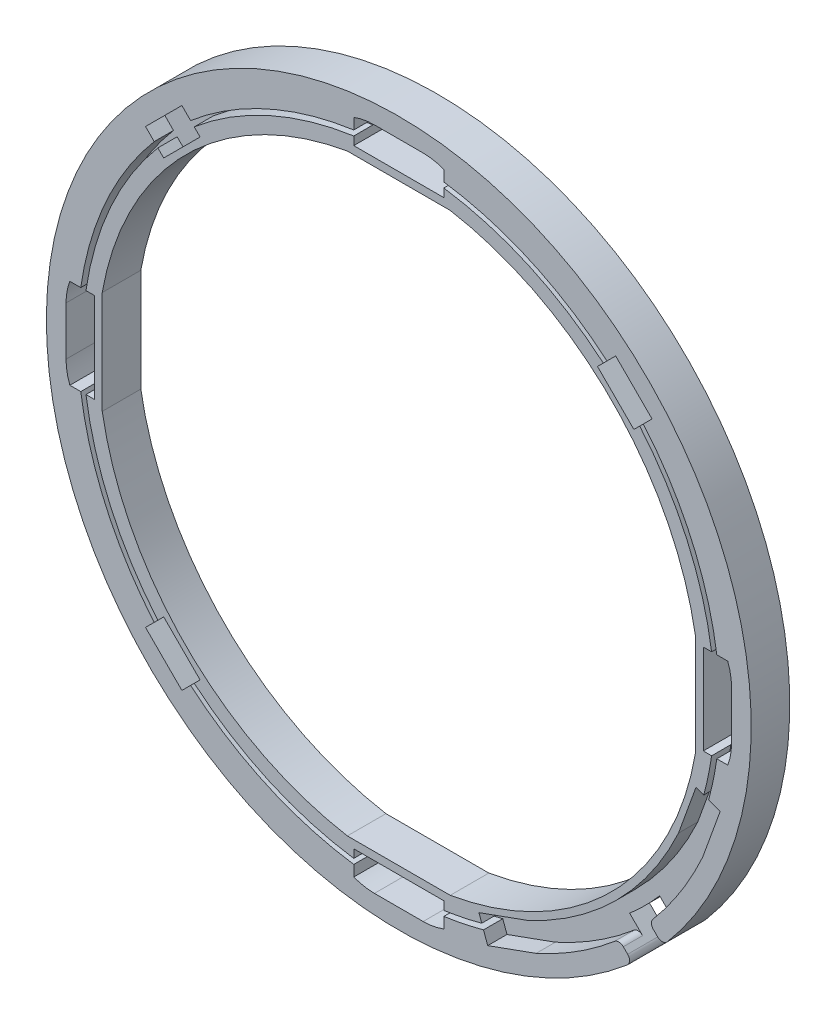
SolidWorks part; units mm, degrees
ref_plane "Front Plane" through (0, 0, 0) normal (0, 0, 1) x (1, 0, 0)
ref_plane "Top Plane" through (0, 0, 0) normal (0, 1, 0) x (1, 0, 0)
ref_plane "Right Plane" through (0, 0, 0) normal (1, 0, 0) x (0, 0, -1)
sketch "Sketch2" plane through (0, 0, 0) normal (0, 0, 1) x (1, 0, 0)
  line L0 (0, 0) -> (0, 31.8027) construction
  line L1 (-4, 23.0556) -> (4, 23.0556)
  line L2 (23.0556, 4) -> (23.0556, -4)
  line L3 (4, -23.0556) -> (-4, -23.0556)
  line L4 (-23.0556, -4) -> (-23.0556, 4)
  circle A0 centre (0, 0) radius 27.4
  arc A1 (-4, 23.0556) -> (-23.0556, 4) centre (0, 0) ccw
  arc A2 (4, 23.0556) -> (0, 23.4) centre (0, 0) ccw construction
  arc A3 (0, 23.4) -> (-4, 23.0556) centre (0, 0) ccw construction
  arc A4 (23.0556, -4) -> (23.0556, 4) centre (0, 0) ccw construction
  arc A5 (23.0556, 4) -> (4, 23.0556) centre (0, 0) ccw
  arc A6 (-4, -23.0556) -> (4, -23.0556) centre (0, 0) ccw construction
  arc A7 (4, -23.0556) -> (23.0556, -4) centre (0, 0) ccw
  arc A8 (-23.0556, 4) -> (-23.0556, -4) centre (0, 0) ccw construction
  arc A9 (-23.0556, -4) -> (-4, -23.0556) centre (0, 0) ccw
  dimension "D1" = 54.8
  dimension "D4" = 4
extrude "Extrude1" add sketch "Sketch2" along normal blind 3
ref_plane "Plane1" through (0, 0, 3) normal (0, 0, 1) x (1, 0, 0)
sketch "Sketch4" plane through (0, 0, 0) normal (1, 0, 0) x (0, 0, -1)
  line L0 (-3, 27.4) -> (-3.3, 23.1028)
  line L1 (-3.3, 23.1028) -> (-3.3, 0)
  line L2 (0, 0) -> (-3, 0) construction
  line L3 (-3, 27.4) -> (-3, -27.4) construction
  line L4 (-3.3, 0) -> (-3, 0)
  line L5 (-3, 0) -> (-3, 27.4)
  dimension "D1" = 0.3
revolve "Cut-Revolve1" [suppressed] cut sketch "Sketch4" angle 360 about L2
sketch "Sketch3" plane through (0, 0, 3) normal (0, 0, 1) x (1, 0, 0)
  line L0 (0, 0) -> (0, 29.437) construction
  line L1 (0, 0) -> (35.1715, 0) construction
  line L2 (-1.8939, 25.8711) -> (1.8939, 25.8711)
  line L3 (3.5, 25.5741) -> (3.5, 23.6711)
  line L4 (3.5, 23.6711) -> (-3.5, 23.6711)
  line L5 (1.8939, 25.8711) -> (3.5, 25.8711) construction
  line L6 (3.5, 25.8711) -> (3.5, 25.5741) construction
  line L7 (-3.5, 25.8711) -> (-3.5, 25.5741) construction
  line L8 (-1.8939, 25.8711) -> (-3.5, 25.8711) construction
  line L9 (-3.5, 25.5741) -> (-3.5, 23.6711)
  line L10 (23.6711, -3.5) -> (23.6711, 3.5)
  line L11 (25.5741, 3.5) -> (23.6711, 3.5)
  line L12 (25.8711, 1.8939) -> (25.8711, -1.8939)
  line L13 (25.5741, -3.5) -> (23.6711, -3.5)
  line L14 (-3.5, -23.6711) -> (3.5, -23.6711)
  line L15 (3.5, -25.5741) -> (3.5, -23.6711)
  line L16 (1.8939, -25.8711) -> (-1.8939, -25.8711)
  line L17 (-3.5, -25.5741) -> (-3.5, -23.6711)
  line L18 (-23.6711, 3.5) -> (-23.6711, -3.5)
  line L19 (-25.5741, -3.5) -> (-23.6711, -3.5)
  line L20 (-25.8711, -1.8939) -> (-25.8711, 1.8939)
  line L21 (-25.5741, 3.5) -> (-23.6711, 3.5)
  arc A0 (1.8939, 25.8711) -> (3.5, 25.5741) centre (1.8939, 21.3807) cw
  arc A1 (-1.8939, 25.8711) -> (-3.5, 25.5741) centre (-1.8939, 21.3807) ccw
  arc A2 (25.8711, 1.8939) -> (25.5741, 3.5) centre (21.3807, 1.8939) ccw
  arc A3 (25.8711, -1.8939) -> (25.5741, -3.5) centre (21.3807, -1.8939) cw
  arc A4 (1.8939, -25.8711) -> (3.5, -25.5741) centre (1.8939, -21.3807) ccw
  arc A5 (-1.8939, -25.8711) -> (-3.5, -25.5741) centre (-1.8939, -21.3807) cw
  arc A6 (-25.8711, -1.8939) -> (-25.5741, -3.5) centre (-21.3807, -1.8939) ccw
  arc A7 (-25.8711, 1.8939) -> (-25.5741, 3.5) centre (-21.3807, 1.8939) cw
  point P12 (0, 23.6711)
  point P13 (0, 25.8711)
  dimension "D1" = 2.2
  dimension "D2" = 7
  dimension "D3" = 4
extrude "Extrude2" cut sketch "Sketch3" against normal blind 3
sketch "Sketch5" plane through (0, 0, 3) normal (0, 0, 1) x (1, 0, 0)
  line L0 (0, 23.6711) -> (0, 25.8711) construction
  line L3 (1.8939, 25.8711) -> (-1.8939, 25.8711) construction
  line L4 (-3.5, 23.6711) -> (3.5, 23.6711) construction
  circle A0 centre (0, 0) radius 24.7711 construction
  circle A1 centre (0, 0) radius 24.5711
  circle A2 centre (0, 0) radius 24.9711
  point P9 (0, 24.7711)
  dimension "D1" = 0.2
  dimension "D2" = 0.2
extrude "Extrude3" cut sketch "Sketch5" against normal blind 1.5
sketch "Sketch8" plane through (0, 0, 3) normal (0, 0, 1) x (1, 0, 0)
  line L0 (0, 0) -> (22.1886, -22.1886) construction
  line L1 (0, 0) -> (20.1949, 0) construction
  line L2 (18.2822, -17.0094) -> (16.5335, -15.2607)
  line L3 (16.5335, -15.2607) -> (17.2395, -14.5547)
  line L4 (17.2395, -14.5547) -> (18.9486, -16.2638)
  line L5 (18.9486, -16.2638) -> (18.2822, -17.0094)
  line L6 (14.5547, -17.2395) -> (16.2638, -18.9486)
  line L7 (15.2607, -16.5335) -> (14.5547, -17.2395)
  line L8 (17.0094, -18.2822) -> (15.2607, -16.5335)
  line L9 (16.2638, -18.9486) -> (17.0094, -18.2822)
  arc A1 (3.5, -24.7246) -> (24.7246, -3.5) centre (0, 0) ccw construction
  dimension "D1" = 45
  dimension "D2" = 1
  dimension "D3" = 1.8
extrude "Extrude5" [suppressed] cut sketch "Sketch8" against normal blind 5
sketch "Sketch6" plane through (0, 0, 3) normal (0, 0, 1) x (1, 0, 0)
  line L0 (0, 0) -> (21.6921, 21.6921) construction
  line L1 (0, 0) -> (0, 29.7187) construction
  line L2 (0, 0) -> (-21.6921, 21.6921) construction
  line L3 (16.8628, 19.6912) -> (19.6912, 16.8628)
  line L4 (19.6912, 16.8628) -> (18.277, 15.4486)
  line L5 (18.277, 15.4486) -> (15.4486, 18.277)
  line L6 (17.6573, 17.6573) -> (17.3744, 17.3744) construction
  line L7 (16.8628, 19.6912) -> (15.4486, 18.277)
  line L8 (-19.6912, 16.8628) -> (-18.277, 15.4486)
  line L9 (-16.8628, 19.6912) -> (-19.6912, 16.8628)
  line L10 (-16.8628, 19.6912) -> (-15.4486, 18.277)
  line L11 (-18.277, 15.4486) -> (-15.4486, 18.277)
  line L12 (0, 0) -> (39.4072, 0) construction
  line L13 (19.6912, -16.8628) -> (18.277, -15.4486)
  line L14 (16.8628, -19.6912) -> (19.6912, -16.8628)
  line L15 (16.8628, -19.6912) -> (15.4486, -18.277)
  line L16 (18.277, -15.4486) -> (15.4486, -18.277)
  line L17 (-16.8628, -19.6912) -> (-19.6912, -16.8628)
  line L18 (-16.8628, -19.6912) -> (-15.4486, -18.277)
  line L19 (-18.277, -15.4486) -> (-15.4486, -18.277)
  line L20 (-19.6912, -16.8628) -> (-18.277, -15.4486)
  line L21 (0, 0) -> (34.2783, 7.6346) construction
  line L22 (24.9865, -6.912) -> (23.1057, -6.2317)
  line L23 (23.6258, -10.6735) -> (24.9865, -6.912)
  line L24 (23.6258, -10.6735) -> (21.745, -9.9931)
  line L25 (23.1057, -6.2317) -> (21.745, -9.9931)
  line L26 (0, 0) -> (11.4166, -11.4166) construction
  line L27 (10.6735, -23.6258) -> (6.912, -24.9865)
  line L28 (10.6735, -23.6258) -> (9.9931, -21.745)
  line L29 (6.2317, -23.1057) -> (9.9931, -21.745)
  line L30 (6.912, -24.9865) -> (6.2317, -23.1057)
  arc A0 (24.7246, 3.5) -> (3.5, 24.7246) centre (0, 0) ccw construction
  point P21 (16.8628, 16.8628)
  point P22 (18.277, 18.277)
  dimension "D1" = 45
  dimension "D2" = 2
  dimension "D3" = 4
extrude "Extrude4" cut sketch "Sketch6" against normal blind 1.5 contours L8 L11 L10 L9 | L3 L7 L5 L4 | L20 L17 L18 L19 | L30 L27 L28 L29 | L22 L25 L24 L23
ref_plane "Plane3" through (0, 0, 0) normal (0.7071, 0.7071, 0) x (0.7071, -0.7071, 0)
sketch "Sketch13" plane through (0, 0, 3) normal (0, 0, 1) x (1, 0, 0)
  line L0 (0, 0) -> (25.3776, -25.3776) construction
  line L1 (0, 0) -> (11.536, 0) construction
  line L4 (19.9758, -17.6423) -> (18.7854, -16.452)
  line L5 (18.7854, -16.452) -> (17.9366, -17.3734)
  line L6 (17.6423, -19.9758) -> (16.452, -18.7854)
  line L9 (16.452, -18.7854) -> (17.3734, -17.9366)
  line L10 (17.6423, -19.9758) -> (19.1802, -21.5136)
  line L11 (19.1802, -21.5136) -> (21.5136, -19.1802)
  line L12 (21.5136, -19.1802) -> (19.9758, -17.6423)
  line L14 (17.9366, -17.3734) -> (17.3734, -17.9366)
  arc A0 (3.5, -24.7246) -> (6.5866, -24.0868) centre (0, 0) ccw construction
  circle A1 centre (0, 0) radius 27.4 construction
  point P5 (17.9366, -17.3734)
  point P19 (19.3747, -19.3747)
  dimension "D1" = 45
  dimension "D2" = 3.3
extrude "Extrude11" cut sketch "Sketch13" against normal blind 3.8
sketch "Sketch14" plane through (0, 0, 3) normal (0, 0, 1) x (1, 0, 0)
  line L0 (3.5, -24.3206) -> (3.5, -24.7246) construction
  line L1 (10.6735, -23.6258) -> (10.2798, -22.5374)
  line L2 (10.6735, -23.6258) -> (10.348, -22.7261) construction
  line L3 (16.452, -18.7854) -> (18.1728, -20.5063) construction
  line L4 (10.2798, -22.5374) -> (9.9931, -21.745)
  line L5 (10.2115, -22.3487) -> (9.9931, -21.745) construction
  line L6 (17.1278, -19.4612) -> (16.3102, -18.6437) construction
  line L7 (0, 0) -> (10.8066, -10.8066) construction
  line L8 (23.6258, -10.6735) -> (22.5374, -10.2798)
  line L9 (22.5374, -10.2798) -> (21.745, -9.9931)
  line L10 (18.6437, -16.3102) -> (18.0485, -15.715) construction
  line L11 (20.5063, -18.1728) -> (18.7854, -16.452) construction
  line L12 (17.1278, -19.4612) -> (19.4612, -17.1278)
  line L13 (19.4612, -17.1278) -> (18.6437, -16.3102) construction
  line L14 (16.3102, -18.6437) -> (15.715, -18.0485) construction
  circle A0 centre (0, 0) radius 24.7711 construction
  arc A1 (10.6735, -23.6258) -> (17.1278, -19.4612) centre (0, 0) ccw
  arc A2 (9.9931, -21.745) -> (15.715, -18.0485) centre (0, 0) ccw
  arc A3 (23.6258, -10.6735) -> (19.4612, -17.1278) centre (0, 0) cw
  arc A4 (21.745, -9.9931) -> (18.0485, -15.715) centre (0, 0) cw
  arc A5 (15.715, -18.0485) -> (18.0485, -15.715) centre (0, 0) ccw
  point P0 (3.5, -24.5226)
extrude "Extrude12" cut sketch "Sketch14" against normal up to surface (1.5 mm away) up to face at (15.9128, -15.9128, 1.5)
sketch "Sketch12" plane through (0, 0, 0) normal (0.7071, 0.7071, 0) x (0.7071, -0.7071, 0)
  line L0 (24.8952, -1.4993) -> (26.3085, -3.1963)
  line L1 (26.3085, -3.1963) -> (24.7674, -3.1963)
  line L2 (24.7674, -3.1963) -> (24.8952, -1.4993)
extrude "Extrude10" [suppressed] cut sketch "Sketch12" against normal mid plane 3.8
fillet "Fillet1" radius 0.5 4 edges at (20.5063, -18.1728, 1.5) (18.1728, -20.5063, 1.5) (17.1278, -19.4612, 2.25) (19.4612, -17.1278, 2.25)
